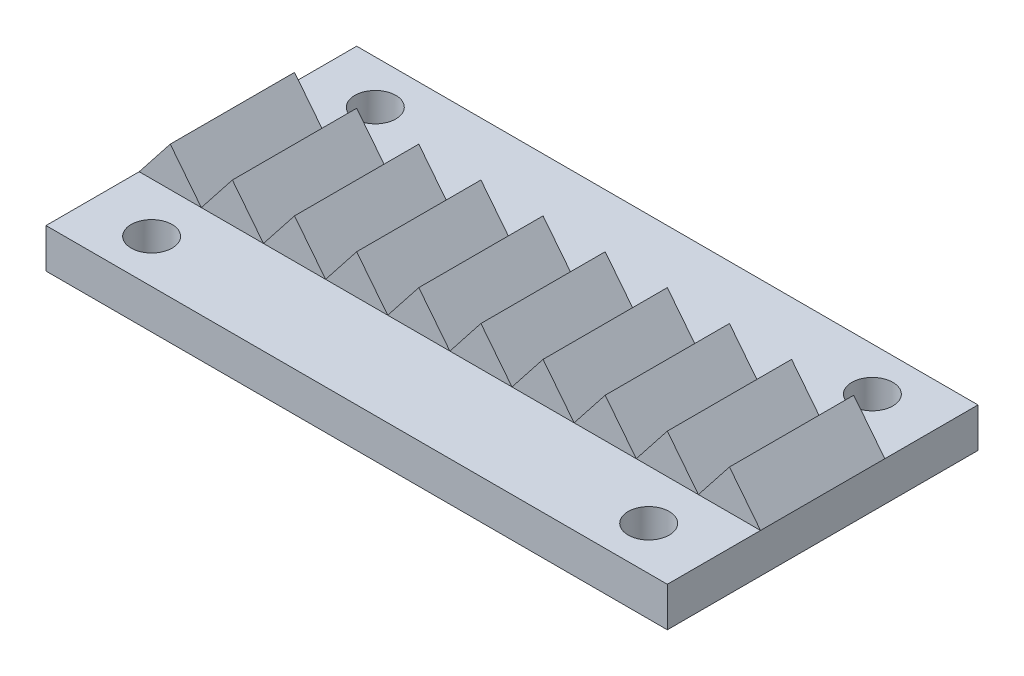
SolidWorks part; units mm, degrees
material "ABS"
ref_plane "Front Plane" through (0, 0, 0) normal (0, 0, 1) x (1, 0, 0)
ref_plane "Top Plane" through (0, 0, 0) normal (0, 1, 0) x (1, 0, 0)
ref_plane "Right Plane" through (0, 0, 0) normal (1, 0, 0) x (0, 0, -1)
sketch "Sketch1" plane through (0, 0, 0) normal (0, 1, 0) x (1, 0, 0)
  line L1 (0, 0) -> (50, 0)
  line L2 (0, 0) -> (0, 25)
  line L3 (0, 25) -> (50, 25)
  line L4 (50, 0) -> (50, 25)
  dimension "D1" = 50
  dimension "D2" = 25
extrude "Boss-Extrude1" add sketch "Sketch1" along normal blind 3.175
sketch "Sketch2" plane through (0, 3.175, 0) normal (0, 1, 0) x (1, 0, 0)
  line L0 (25, 25) -> (25, 0) construction
  line L1 (50, 25) -> (0, 25) construction
  line L2 (0, 0) -> (50, 0) construction
  line L3 (0, 12.5) -> (50, 12.5) construction
  line L4 (0, 25) -> (0, 0) construction
  line L5 (50, 0) -> (50, 25) construction
  point P12 (5, 21.5)
  point P14 (45, 21.5)
  point P16 (45, 3.5)
  point P17 (5, 3.5)
  dimension "D1" = 20
  dimension "D2" = 9
hole_wizard "M4x0.7 Tapped Hole1" positions "3DSketch1" profile "Sketch3" tap size "M4x0.7" standard "ANSI Metric"
sketch3d "3DSketch1"
  point P0 (5, 3.175, -21.5)
  point P3 (45, 3.175, -21.5)
  point P6 (5, 3.175, -3.5)
  point P9 (45, 3.175, -3.5)
sketch "Sketch3" plane through (5, 3.175, -21.5) normal (1, 0, 0) x (0, 0, 1)
  line L0 (0, 0) -> (0, 11.0914)
  line L1 (0, 11.0914) -> (1.65, 10.1)
  line L2 (1.65, 10.1) -> (1.65, 0)
  line L5 (1.65, 0) -> (0, 0)
  line L10 (0, 11.0914) -> (-1.65, 10.1) construction
  line L11 (0, -6.35) -> (0, 107.95) construction
  dimension "Tap Drill Dia." = 3.3
  dimension "Tap Drill Depth" = 10.1
  dimension "Drill Angle" = 118
sketch "Sketch4" plane through (0, 0, 0) normal (0, 0, 1) x (1, 0, 0)
  line L0 (25, 3.175) -> (25, 6.35) construction
  line L1 (27.5, 3.175) -> (27.5, 6.35) construction
  line L2 (0, 3.175) -> (50, 3.175) construction
  line L3 (25, 3.175) -> (30, 3.175)
  line L4 (0, 3.175) -> (50, 3.175) construction
  line L5 (25, 3.175) -> (27.5, 6.35)
  line L6 (27.5, 6.35) -> (30, 3.175)
  line L7 (32.5, 6.35) -> (35, 3.175)
  line L8 (30, 3.175) -> (35, 3.175)
  line L9 (30, 3.175) -> (32.5, 6.35)
  line L10 (37.5, 6.35) -> (40, 3.175)
  line L11 (35, 3.175) -> (40, 3.175)
  line L12 (35, 3.175) -> (37.5, 6.35)
  line L13 (42.5, 6.35) -> (45, 3.175)
  line L14 (40, 3.175) -> (45, 3.175)
  line L15 (40, 3.175) -> (42.5, 6.35)
  line L16 (47.5, 6.35) -> (50, 3.175)
  line L17 (45, 3.175) -> (50, 3.175)
  line L18 (45, 3.175) -> (47.5, 6.35)
  line L19 (27.5, 6.35) -> (32.5, 6.35) construction
  line L20 (22.5, 6.35) -> (25, 3.175)
  line L21 (20, 3.175) -> (25, 3.175)
  line L22 (20, 3.175) -> (22.5, 6.35)
  line L23 (17.5, 6.35) -> (20, 3.175)
  line L24 (15, 3.175) -> (20, 3.175)
  line L25 (15, 3.175) -> (17.5, 6.35)
  line L26 (12.5, 6.35) -> (15, 3.175)
  line L27 (10, 3.175) -> (15, 3.175)
  line L28 (10, 3.175) -> (12.5, 6.35)
  line L29 (7.5, 6.35) -> (10, 3.175)
  line L30 (5, 3.175) -> (10, 3.175)
  line L31 (5, 3.175) -> (7.5, 6.35)
  line L32 (2.5, 6.35) -> (5, 3.175)
  line L33 (0, 3.175) -> (5, 3.175)
  line L34 (0, 3.175) -> (2.5, 6.35)
  line L35 (27.5, 6.35) -> (22.5, 6.35) construction
  line M10 (50, 3.175) -> (0, 3.175)
  dimension "D1" = 3.175
  dimension "D2" = 3.175
  dimension "D3" = 2.5
  dimension "D4" = 5
  dimension "D6" = 5
  dimension "D8" = 5
  dimension "D5" = 5
  dimension "D7" = 6
extrude "Boss-Extrude2" add sketch "Sketch4" against normal blind 10 from offset 7.5 contours L34 L32 M10 | L31 L29 M10 | L28 L26 M10 | L25 L23 M10 | L22 L20 M10 | L6 L5 M10 | L9 L7 M10 | L12 L10 M10 | L15 L13 M10 | L18 L16 M10
